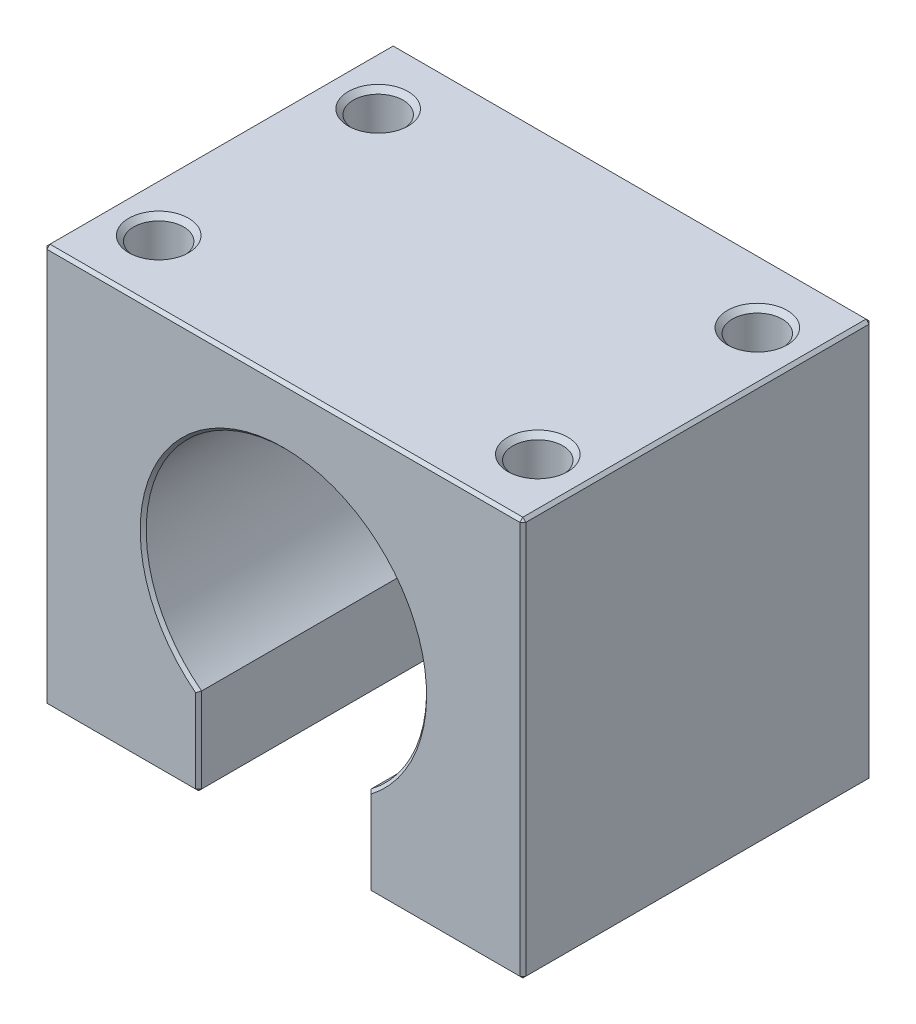
SolidWorks part; units mm, degrees
material "1060 Alloy"
ref_plane "Front Plane" through (0, 0, 0) normal (0, 0, 1) x (1, 0, 0)
ref_plane "Top Plane" through (0, 0, 0) normal (0, 1, 0) x (1, 0, 0)
ref_plane "Right Plane" through (0, 0, 0) normal (1, 0, 0) x (0, 0, -1)
sketch "Sketch1" plane through (0, 0, 0) normal (0, 0, 1) x (1, 0, 0)
  line L0 (-8.5, 0) -> (-8.5, -40) construction
  line L1 (0, 0) -> (-24, 0) construction
  line L2 (0, 0) -> (0, -40) construction
  line L3 (0, -40) -> (-24, -40) construction
  line L4 (-24, 0) -> (-24, -40) construction
  line L5 (-24, -20) -> (-8.5, -20) construction
  line L6 (24, 0) -> (-24, 0)
  line L7 (-24, 0) -> (-24, -40)
  line L8 (-24, -40) -> (-8.5, -40)
  line L9 (-8.5, -40) -> (-8.5, -31.1872)
  line L10 (8.5, -40) -> (8.5, -31.1872)
  line L11 (24, -40) -> (8.5, -40)
  line L12 (24, 0) -> (24, -40)
  circle A0 centre (0, -20) radius 14.05 construction
  arc A1 (8.5, -31.1872) -> (-8.5, -31.1872) centre (0, -20) ccw
  dimension "D5" = 28.1
  dimension "D1" = 24
  dimension "D2" = 40
  dimension "D3" = 8.5
  dimension "D4" = 20
extrude "Boss-Extrude1" add sketch "Sketch1" along normal blind 35
chamfer "Chamfer2" distance 0.3 angle 45 22 edges at (-8.5, -35.5936, 0) (-16.25, -40, 0) (16.25, -40, 0) (8.5, -35.5936, 0) (-24, -20, 0) (-24, -40, 17.5) (8.5, -40, 17.5) (0, 0, 0) (-24, 0, 17.5) (-8.5, -40, 17.5) (-8.5, -35.5936, 35) (-16.25, -40, 35) (-24, -20, 35) (8.5, -35.5936, 35) (16.25, -40, 35) (24, -40, 17.5) (24, -20, 0) (24, 0, 17.5) (0, 0, 35) (24, -20, 35) (0, -5.95, 35) (0, -5.95, 0)
sketch "Sketch2" plane through (0, 0, 0) normal (0, 1, 0) x (1, 0, 0)
  line L0 (0, 0) -> (0, -35) construction
  line L1 (23.7, -35) -> (-23.7, -35) construction
  line L3 (-19, -6.5) -> (19, -6.5) construction
  line L4 (-19, -6.5) -> (-19, -28.5) construction
  line L5 (-19, -28.5) -> (19, -28.5) construction
  line L6 (19, -6.5) -> (19, -28.5) construction
  line L7 (-19, -6.5) -> (19, -28.5) construction
  line L8 (-19, -28.5) -> (19, -6.5) construction
  line L9 (-19, -17.5) -> (19, -17.5) construction
  circle A0 centre (-19, -6.5) radius 2.5
  circle A1 centre (19, -6.5) radius 2.5
  circle A2 centre (19, -28.5) radius 2.5
  circle A3 centre (-19, -28.5) radius 2.5
  point P5 (0, -17.5)
  dimension "D3" = 5
  dimension "D1" = 38
  dimension "D2" = 22
extrude "Cut-Extrude1" cut sketch "Sketch2" against normal blind 17
sketch "Sketch3" plane through (0, 0, 0) normal (0, 0, -1) x (-1, 0, 0)
  line L0 (0, 0) -> (0, -40) construction
  line L1 (0, -20) -> (-20, -40) construction
  line L2 (-24, -20) -> (24, -20) construction
  line L3 (-24, -39.7) -> (-24, -0.3) construction
  line L4 (-8.8, -40) -> (-23.7, -40) construction
  line L5 (0, -20) -> (20, -40) construction
  line L6 (24, -0.3) -> (24, -39.7) construction
  line L7 (-24, -33.435) -> (24, -33.435) construction
  line L8 (-24, -6.565) -> (24, -6.565) construction
  circle A0 centre (0, -20) radius 19 construction
  circle A1 centre (-13.435, -33.435) radius 2.5
  circle A2 centre (13.435, -33.435) radius 2.5
  circle A3 centre (13.435, -6.565) radius 2.5
  circle A4 centre (-13.435, -6.565) radius 2.5
  circle A5 centre (-19, -20) radius 2.5
  circle A6 centre (19, -20) radius 2.5
  dimension "D2" = 38
  dimension "D4" = 5
  dimension "D1" = 40
  dimension "D3" = 45
  dimension "D5" = 13.435
extrude "Cut-Extrude2" cut sketch "Sketch3" against normal blind 20
chamfer "Chamfer3" distance 0.5 angle 45 9 edges at (16.5, -20, 0) (10.935, -33.435, 0) (-10.935, -33.435, 0) (-16.5, -20, 0) (-15.935, -6.565, 0) (16.5, 0, 28.5) (21.5, 0, 6.5) (-16.5, 0, 28.5) (-21.5, 0, 6.5)
